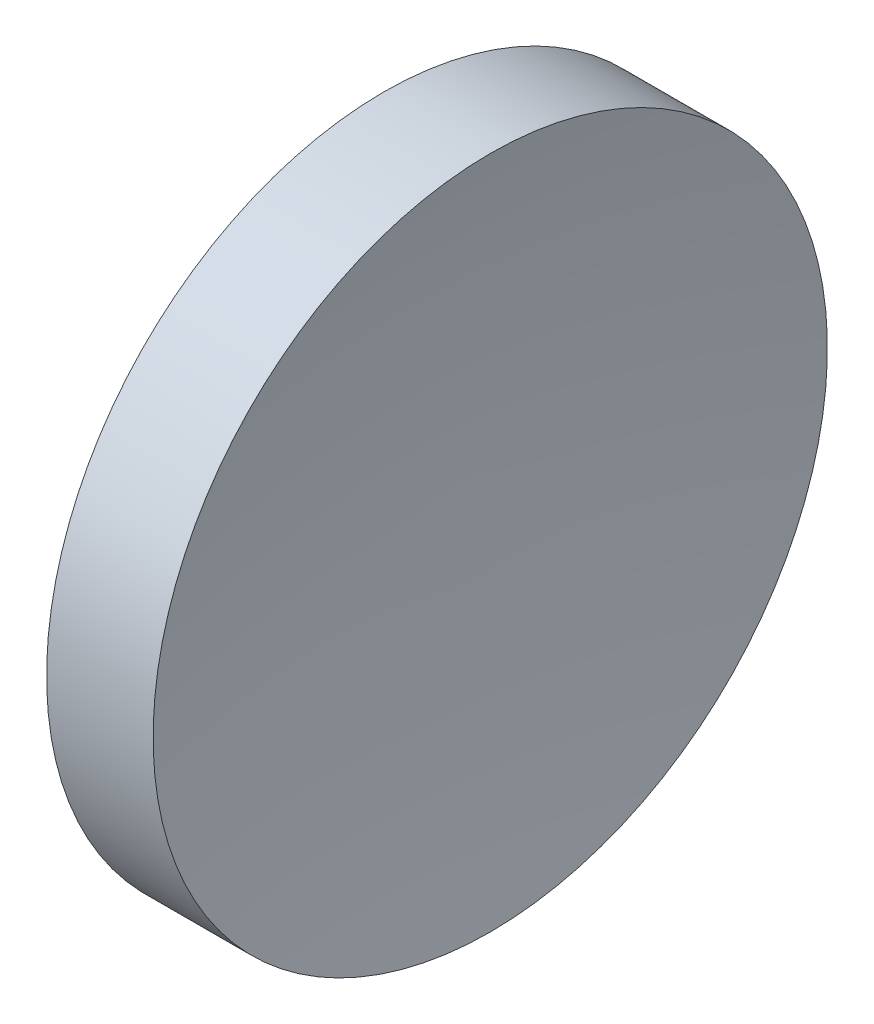
SolidWorks part; units mm, degrees
ref_plane "前视基准面" through (0, 0, 0) normal (0, 0, 1) x (1, 0, 0)
ref_plane "上视基准面" through (0, 0, 0) normal (0, 1, 0) x (1, 0, 0)
ref_plane "右视基准面" through (0, 0, 0) normal (1, 0, 0) x (0, 0, -1)
sketch "草图1" plane through (0, 0, 0) normal (0, 0, 1) x (1, 0, 0)
  line L0 (89.8587, 52.1781) -> (104.0854, 52.1781) construction
  line L1 (97.0904, 52.1781) -> (95.0904, 52.1781)
  line L3 (96.0904, 64.8781) -> (98.097, 64.8781)
  line L4 (96.0904, 64.8781) -> (94.0839, 64.8781)
  arc A0 (95.0904, 52.1781) -> (94.0839, 64.8781) centre (23.2939, 52.8777) ccw
  arc A1 (98.097, 64.8781) -> (97.0904, 52.1781) centre (168.887, 52.8777) ccw
revolve "旋转1" add sketch "草图1" angle 360 about L0
